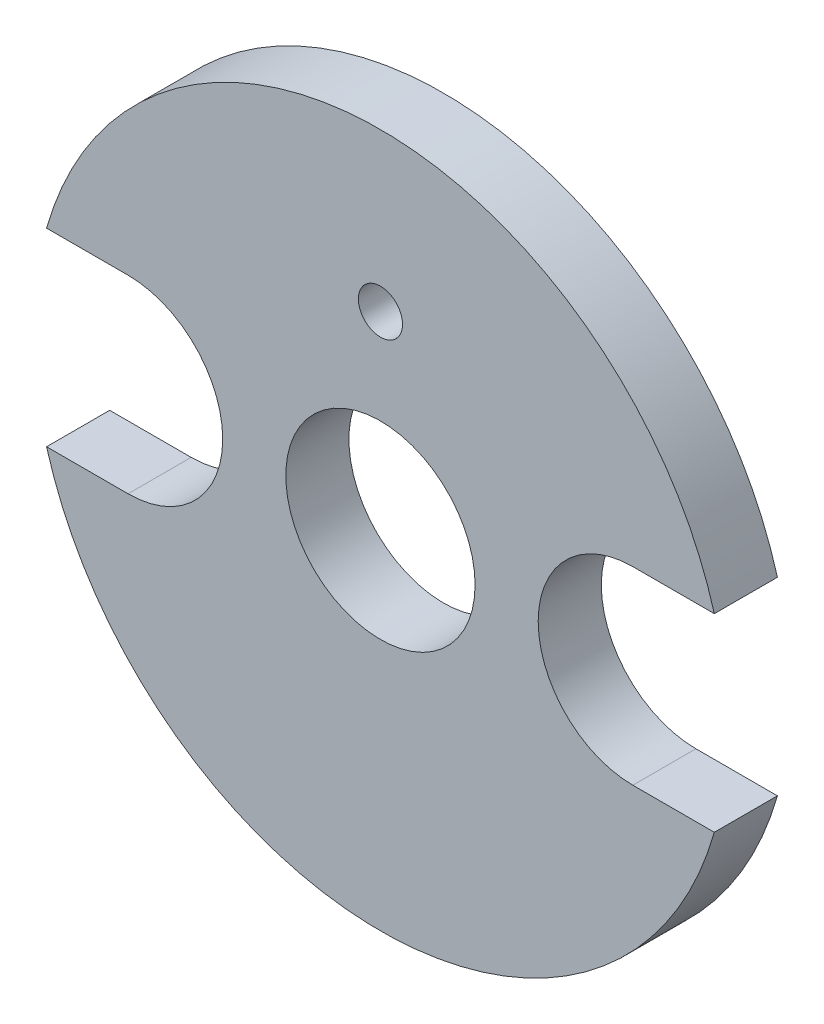
SolidWorks part; units mm, degrees
material "Acrylic (Medium-high impact)"
ref_plane "Front Plane" through (0, 0, 0) normal (0, 0, 1) x (1, 0, 0)
ref_plane "Top Plane" through (0, 0, 0) normal (0, 1, 0) x (1, 0, 0)
ref_plane "Right Plane" through (0, 0, 0) normal (1, 0, 0) x (0, 0, -1)
sketch "Model" plane through (0, 0, 0) normal (0, 0, 1) x (1, 0, 0)
  line L695 (-8, 3) -> (-10.583, 3)
  line L696 (-8, -3) -> (-10.583, -3)
  line L697 (8, -3) -> (10.583, -3)
  line L698 (8, 3) -> (10.583, 3)
  circle A0 centre (0, 6) radius 0.7
  arc A317 (10.583, 3) -> (-10.583, 3) centre (0, 0) ccw
  arc A318 (-8, -3) -> (-8, 3) centre (-8, 0) ccw
  arc A319 (8, 3) -> (8, -3) centre (8, 0) ccw
  arc A320 (-10.583, -3) -> (10.583, -3) centre (0, 0) ccw
  circle A321 centre (0, 0) radius 3
  dimension "D1" = 11
  dimension "D2" = 3
  dimension "D4" = 1.4
  dimension "D3" = 8
  dimension "D5" = 6
extrude "Boss-Extrude1" add sketch "Model" along normal blind 2
